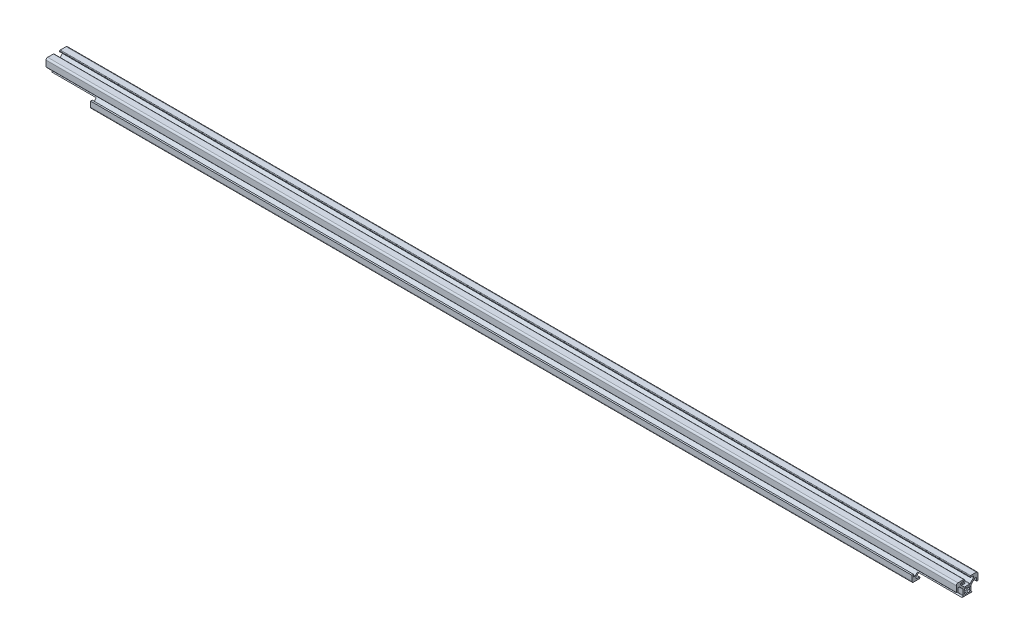
SolidWorks part; units mm, degrees
ref_plane "Front Plane" through (0, 0, 0) normal (0, 0, 1) x (1, 0, 0)
ref_plane "Top Plane" through (0, 0, 0) normal (0, 1, 0) x (1, 0, 0)
ref_plane "Right Plane" through (0, 0, 0) normal (1, 0, 0) x (0, 0, -1)
sketch "Sketch1" plane through (0, 0, 0) normal (0, 0, 1) x (1, 0, 0)
  line L0 (0, 0) -> (838.4, 0)
  dimension "D1" = 838.4
other " C:\\PROGRAM FILES\\SOLIDWORKS CORP\\SOLIDWORKS\\LANG\\ENGLISH\\WELDMENT PROFILES\\DIY PROFILES\\METRIC AL EXTRUSION\\20-2020 PROFILE - IS MISSING(1)"
ref_plane "Plane1" through (0, 0, 0) normal (1, 0, 0) x (0, 1, 0)
sketch "Sketch122" plane through (0, 0, 0) normal (1, 0, 0) x (0, 1, 0)
  line L0 (9.8952, 3.5708) -> (9.4112, 3.5708)
  line L1 (8.9032, 4.0788) -> (8.9032, 6.4278)
  line L2 (10.4032, 4.0788) -> (10.4032, 9.4408)
  line L3 (4.0582, -1.4431) -> (4.0582, 3.3247)
  line L4 (7.6693, 6.9358) -> (8.3952, 6.9358)
  line L5 (7.3101, 6.787) -> (4.207, 3.6839)
  line L6 (9.8952, -1.6892) -> (9.4112, -1.6892)
  line L7 (10.4032, -2.1972) -> (10.4032, -7.5592)
  line L8 (8.9032, -2.1972) -> (8.9032, -4.5462)
  line L9 (7.6693, -5.0542) -> (8.3952, -5.0542)
  line L10 (7.3101, -4.9054) -> (4.207, -1.8023)
  line L11 (2.5281, -1.3637) -> (2.7077, -1.1841)
  line L12 (-2.2268, 10.4328) -> (-2.2268, 9.9488)
  line L13 (-2.7348, 10.9408) -> (-8.0968, 10.9408)
  line L14 (-2.7348, 9.4408) -> (-5.0838, 9.4408)
  line L15 (2.7871, 4.5958) -> (-1.9807, 4.5958)
  line L16 (-5.5918, 8.2069) -> (-5.5918, 8.9328)
  line L17 (-5.443, 7.8477) -> (-2.3399, 4.7446)
  line L18 (3.0332, 10.4328) -> (3.0332, 9.9488)
  line L19 (3.5412, 10.9408) -> (8.9032, 10.9408)
  line L20 (3.5412, 9.4408) -> (5.8902, 9.4408)
  line L21 (6.3982, 8.2069) -> (6.3982, 8.9328)
  line L22 (6.2494, 7.8477) -> (3.1463, 4.7446)
  line L23 (2.7077, 3.0657) -> (2.5281, 3.2453)
  line L24 (-9.0888, -1.6892) -> (-8.6048, -1.6892)
  line L25 (-9.5968, -2.1972) -> (-9.5968, -7.5592)
  line L26 (-8.0968, -2.1972) -> (-8.0968, -4.5462)
  line L27 (-3.2518, 3.3247) -> (-3.2518, -1.4431)
  line L28 (-6.8629, -5.0542) -> (-7.5888, -5.0542)
  line L29 (-6.5037, -4.9054) -> (-3.4006, -1.8023)
  line L30 (-9.0888, 3.5708) -> (-8.6048, 3.5708)
  line L31 (-9.5968, 4.0788) -> (-9.5968, 9.4408)
  line L32 (-8.0968, 4.0788) -> (-8.0968, 6.4278)
  line L33 (-6.8629, 6.9358) -> (-7.5888, 6.9358)
  line L34 (-6.5037, 6.787) -> (-3.4006, 3.6839)
  line L35 (-1.7217, 3.2453) -> (-1.9013, 3.0657)
  line L36 (3.0332, -8.5512) -> (3.0332, -8.0672)
  line L37 (3.5412, -9.0592) -> (8.9032, -9.0592)
  line L38 (3.5412, -7.5592) -> (5.8902, -7.5592)
  line L39 (-1.9807, -2.7142) -> (2.7871, -2.7142)
  line L40 (6.3982, -6.3253) -> (6.3982, -7.0512)
  line L41 (6.2494, -5.9661) -> (3.1463, -2.863)
  line L42 (-2.2268, -8.5512) -> (-2.2268, -8.0672)
  line L43 (-2.7348, -9.0592) -> (-8.0968, -9.0592)
  line L44 (-2.7348, -7.5592) -> (-5.0838, -7.5592)
  line L45 (-5.5918, -6.3253) -> (-5.5918, -7.0512)
  line L46 (-5.443, -5.9661) -> (-2.3399, -2.863)
  line L47 (-1.9013, -1.1841) -> (-1.7217, -1.3637)
  arc A0 (-0.4008, -0.9944) -> (1.2072, -0.9944) centre (0.4032, 0.9408) ccw
  arc A1 (8.9032, 6.4278) -> (8.3952, 6.9358) centre (8.3952, 6.4278) ccw
  arc A2 (7.6693, 6.9358) -> (7.3101, 6.787) centre (7.6693, 6.4278) ccw
  arc A3 (4.207, 3.6839) -> (4.0582, 3.3247) centre (4.5662, 3.3247) ccw
  arc A4 (4.0582, -1.4431) -> (4.207, -1.8023) centre (4.5662, -1.4431) ccw
  arc A5 (7.3101, -4.9054) -> (7.6693, -5.0542) centre (7.6693, -4.5462) ccw
  arc A6 (8.3952, -5.0542) -> (8.9032, -4.5462) centre (8.3952, -4.5462) ccw
  arc A7 (9.4112, -1.6892) -> (8.9032, -2.1972) centre (9.4112, -2.1972) ccw
  arc A8 (10.4032, -2.1972) -> (9.8952, -1.6892) centre (9.8952, -2.1972) ccw
  arc A9 (9.8952, 3.5708) -> (10.4032, 4.0788) centre (9.8952, 4.0788) ccw
  arc A10 (8.9032, 4.0788) -> (9.4112, 3.5708) centre (9.4112, 4.0788) ccw
  arc A11 (1.2072, -0.9944) -> (2.5281, -1.3637) centre (1.9716, -0.8072) ccw
  arc A12 (2.7077, -1.1841) -> (2.3383, 0.1368) centre (2.1512, -0.6276) ccw
  arc A13 (-2.2268, 10.4328) -> (-2.7348, 10.9408) centre (-2.7348, 10.4328) ccw
  arc A14 (-2.7348, 9.4408) -> (-2.2268, 9.9488) centre (-2.7348, 9.9488) ccw
  arc A15 (2.3383, 0.1368) -> (2.3383, 1.7448) centre (0.4032, 0.9408) ccw
  arc A16 (-2.3399, 4.7446) -> (-1.9807, 4.5958) centre (-1.9807, 5.1038) ccw
  arc A17 (-5.0838, 9.4408) -> (-5.5918, 8.9328) centre (-5.0838, 8.9328) ccw
  arc A18 (-5.5918, 8.2069) -> (-5.443, 7.8477) centre (-5.0838, 8.2069) ccw
  arc A19 (3.0332, 9.9488) -> (3.5412, 9.4408) centre (3.5412, 9.9488) ccw
  arc A20 (3.5412, 10.9408) -> (3.0332, 10.4328) centre (3.5412, 10.4328) ccw
  arc A21 (6.3982, 8.9328) -> (5.8902, 9.4408) centre (5.8902, 8.9328) ccw
  arc A22 (6.2494, 7.8477) -> (6.3982, 8.2069) centre (5.8902, 8.2069) ccw
  arc A23 (2.7871, 4.5958) -> (3.1463, 4.7446) centre (2.7871, 5.1038) ccw
  arc A24 (2.3383, 1.7448) -> (2.7077, 3.0657) centre (2.1512, 2.5092) ccw
  arc A25 (2.5281, 3.2453) -> (1.2072, 2.8759) centre (1.9716, 2.6888) ccw
  arc A26 (-9.0888, -1.6892) -> (-9.5968, -2.1972) centre (-9.0888, -2.1972) ccw
  arc A27 (-8.0968, -2.1972) -> (-8.6048, -1.6892) centre (-8.6048, -2.1972) ccw
  arc A28 (1.2072, 2.8759) -> (-0.4008, 2.8759) centre (0.4032, 0.9408) ccw
  arc A29 (-3.4006, -1.8023) -> (-3.2518, -1.4431) centre (-3.7598, -1.4431) ccw
  arc A30 (-8.0968, -4.5462) -> (-7.5888, -5.0542) centre (-7.5888, -4.5462) ccw
  arc A31 (-6.8629, -5.0542) -> (-6.5037, -4.9054) centre (-6.8629, -4.5462) ccw
  arc A32 (-8.6048, 3.5708) -> (-8.0968, 4.0788) centre (-8.6048, 4.0788) ccw
  arc A33 (-9.5968, 4.0788) -> (-9.0888, 3.5708) centre (-9.0888, 4.0788) ccw
  arc A34 (-7.5888, 6.9358) -> (-8.0968, 6.4278) centre (-7.5888, 6.4278) ccw
  arc A35 (-6.5037, 6.787) -> (-6.8629, 6.9358) centre (-6.8629, 6.4278) ccw
  arc A36 (-3.2518, 3.3247) -> (-3.4006, 3.6839) centre (-3.7598, 3.3247) ccw
  arc A37 (-0.4008, 2.8759) -> (-1.7217, 3.2453) centre (-1.1652, 2.6888) ccw
  arc A38 (-1.9013, 3.0657) -> (-1.5319, 1.7448) centre (-1.3448, 2.5092) ccw
  arc A39 (3.0332, -8.5512) -> (3.5412, -9.0592) centre (3.5412, -8.5512) ccw
  arc A40 (3.5412, -7.5592) -> (3.0332, -8.0672) centre (3.5412, -8.0672) ccw
  arc A41 (-1.5319, 1.7448) -> (-1.5319, 0.1368) centre (0.4032, 0.9408) ccw
  arc A42 (3.1463, -2.863) -> (2.7871, -2.7142) centre (2.7871, -3.2222) ccw
  arc A43 (5.8902, -7.5592) -> (6.3982, -7.0512) centre (5.8902, -7.0512) ccw
  arc A44 (6.3982, -6.3253) -> (6.2494, -5.9661) centre (5.8902, -6.3253) ccw
  arc A45 (-2.2268, -8.0672) -> (-2.7348, -7.5592) centre (-2.7348, -8.0672) ccw
  arc A46 (-2.7348, -9.0592) -> (-2.2268, -8.5512) centre (-2.7348, -8.5512) ccw
  arc A47 (-5.5918, -7.0512) -> (-5.0838, -7.5592) centre (-5.0838, -7.0512) ccw
  arc A48 (-5.443, -5.9661) -> (-5.5918, -6.3253) centre (-5.0838, -6.3253) ccw
  arc A49 (-1.9807, -2.7142) -> (-2.3399, -2.863) centre (-1.9807, -3.2222) ccw
  arc A50 (-1.5319, 0.1368) -> (-1.9013, -1.1841) centre (-1.3448, -0.6276) ccw
  arc A51 (-1.7217, -1.3637) -> (-0.4008, -0.9944) centre (-1.1652, -0.8072) ccw
  arc A52 (10.4032, 9.4408) -> (8.9032, 10.9408) centre (8.9032, 9.4408) ccw
  arc A53 (8.9032, -9.0592) -> (10.4032, -7.5592) centre (8.9032, -7.5592) ccw
  arc A54 (-9.5968, -7.5592) -> (-8.0968, -9.0592) centre (-8.0968, -7.5592) ccw
  arc A55 (-8.0968, 10.9408) -> (-9.5968, 9.4408) centre (-8.0968, 9.4408) ccw
  point P157 (0, 0)
sketch "Sketch124" plane through (0, 0, 0) normal (-1, 0, 0) x (0, 0, 1)
  line L12 (0.9408, 0.4032) -> (-7.5592, 0.4032) construction
  line L13 (-9.0592, 3.5412) -> (-9.0592, 8.9032) construction
  line L14 (-9.0592, 3.5782) -> (-7.5592, 3.5782)
  line L15 (-9.0592, 3.5782) -> (-9.0592, -2.7718)
  line L16 (-9.0592, -2.7718) -> (-7.5592, -2.7718)
  line L17 (-7.5592, 3.5782) -> (-7.5592, -2.7718)
  line L18 (-7.5592, -2.7348) -> (-7.5592, -5.0838) construction
  line L19 (-7.5592, 5.8902) -> (-7.5592, 3.5412) construction
  line L20 (0.9408, 0.4032) -> (0.9408, 5.3094) construction
  line L21 (10.9408, -2.7718) -> (9.4408, -2.7718)
  line L22 (9.4408, 3.5782) -> (9.4408, -2.7718)
  line L23 (10.9408, 3.5782) -> (9.4408, 3.5782)
  line L24 (10.9408, 3.5782) -> (10.9408, -2.7718)
  point P12 (-7.5592, 0.4032)
  dimension "D1" = 6.35
extrude "Cut-Extrude1" [suppressed] cut sketch "Sketch124" against normal blind 62
sketch "Sketch125" plane through (0, 0, -9.0592) normal (0, 0, -1) x (-1, 0, 0)
  line L5 (-838.4, -3.2518) -> (0, -3.2518) construction
  line L6 (-838.4, -3.2518) -> (0, -3.2518) construction
  line L7 (-838.4, -9.5968) -> (0, -9.5968) construction
  line L8 (-838.4, -3.2518) -> (-797.4, -3.2518)
  line L9 (-838.4, -3.2518) -> (-838.4, -9.5968)
  line L10 (-838.4, -9.5968) -> (-797.4, -9.5968)
  line L11 (-797.4, -3.2518) -> (-797.4, -9.5968)
  line L13 (0, -3.2518) -> (-41, -3.2518)
  line L14 (0, -3.2518) -> (0, -9.5968)
  line L15 (0, -9.5968) -> (-41, -9.5968)
  line L16 (-41, -3.2518) -> (-41, -9.5968)
  dimension "D1" = 41
extrude "Cut-Extrude2" cut sketch "Sketch125" against normal through all
ref_plane "Plane2" through (0, -2.2268, 9.9488) normal (0, 0, 1) x (1, 0, 0)
sketch "Sketch127" plane through (0, 0, 0) normal (-1, 0, 0) x (0, 0, 1)
  line L0 (-9.0592, -2.7348) -> (-9.0592, -3.2518) construction
  line L1 (-9.0592, -3.2518) -> (-7.5592, -3.2518) construction
  line L2 (-7.5592, -3.2518) -> (-7.5592, -2.7348) construction
  line L3 (-8.0672, -2.2268) -> (-8.5512, -2.2268) construction
  line L4 (9.4408, -2.7348) -> (9.4408, -3.2518) construction
  line L5 (9.4408, -3.2518) -> (10.9408, -3.2518) construction
  line L6 (10.9408, -3.2518) -> (10.9408, -2.7348) construction
  line L7 (10.4328, -2.2268) -> (9.9488, -2.2268) construction
  line L8 (-9.0592, -2.7348) -> (-9.0592, -3.2518)
  line L9 (-9.0592, -3.2518) -> (-7.5592, -3.2518)
  line L10 (-7.5592, -3.2518) -> (-7.5592, -2.7348)
  line L11 (-8.0672, -2.2268) -> (-8.5512, -2.2268)
  line L12 (9.4408, -2.7348) -> (9.4408, -3.2518)
  line L13 (9.4408, -3.2518) -> (10.9408, -3.2518)
  line L14 (10.9408, -3.2518) -> (10.9408, -2.7348)
  line L15 (10.4328, -2.2268) -> (9.9488, -2.2268)
  arc A0 (-7.5592, -2.7348) -> (-8.0672, -2.2268) centre (-8.0672, -2.7348) ccw construction
  arc A1 (-8.5512, -2.2268) -> (-9.0592, -2.7348) centre (-8.5512, -2.7348) ccw construction
  arc A2 (10.9408, -2.7348) -> (10.4328, -2.2268) centre (10.4328, -2.7348) ccw construction
  arc A3 (9.9488, -2.2268) -> (9.4408, -2.7348) centre (9.9488, -2.7348) ccw construction
  arc A4 (-7.5592, -2.7348) -> (-8.0672, -2.2268) centre (-8.0672, -2.7348) ccw
  arc A5 (-8.5512, -2.2268) -> (-9.0592, -2.7348) centre (-8.5512, -2.7348) ccw
  arc A6 (10.9408, -2.7348) -> (10.4328, -2.2268) centre (10.4328, -2.7348) ccw
  arc A7 (9.9488, -2.2268) -> (9.4408, -2.7348) centre (9.9488, -2.7348) ccw
extrude "Cut-Extrude3" cut sketch "Sketch127" against normal up to surface (797.4 mm away)
sketch "Sketch128" plane through (0, -3.2518, 0) normal (0, -1, 0) x (1, 0, 0)
  line L0 (0, 5.6564) -> (0, -3.7749) construction
  line L1 (0, 0.9408) -> (37.8238, 0.9408) construction
  line L2 (41, -1.4431) -> (41, -3.7749) construction
  circle A0 centre (4, 0.9408) radius 1.5
  circle A1 centre (19, 0.9408) radius 1.5
  circle A2 centre (34, 0.9408) radius 1.5
  dimension "D4" = 3
  dimension "D1" = 15
  dimension "D2" = 15
  dimension "D3" = 7
extrude "Cut-Extrude4" cut sketch "Sketch128" against normal through all
ref_plane "Plane3" through (419.2, 0, 0) normal (1, 0, 0) x (0, 0, -1)
mirror "Mirror1" about plane through (419.2, 0, 0) normal (1, 0, 0) of "Cut-Extrude4", "Cut-Extrude3"
